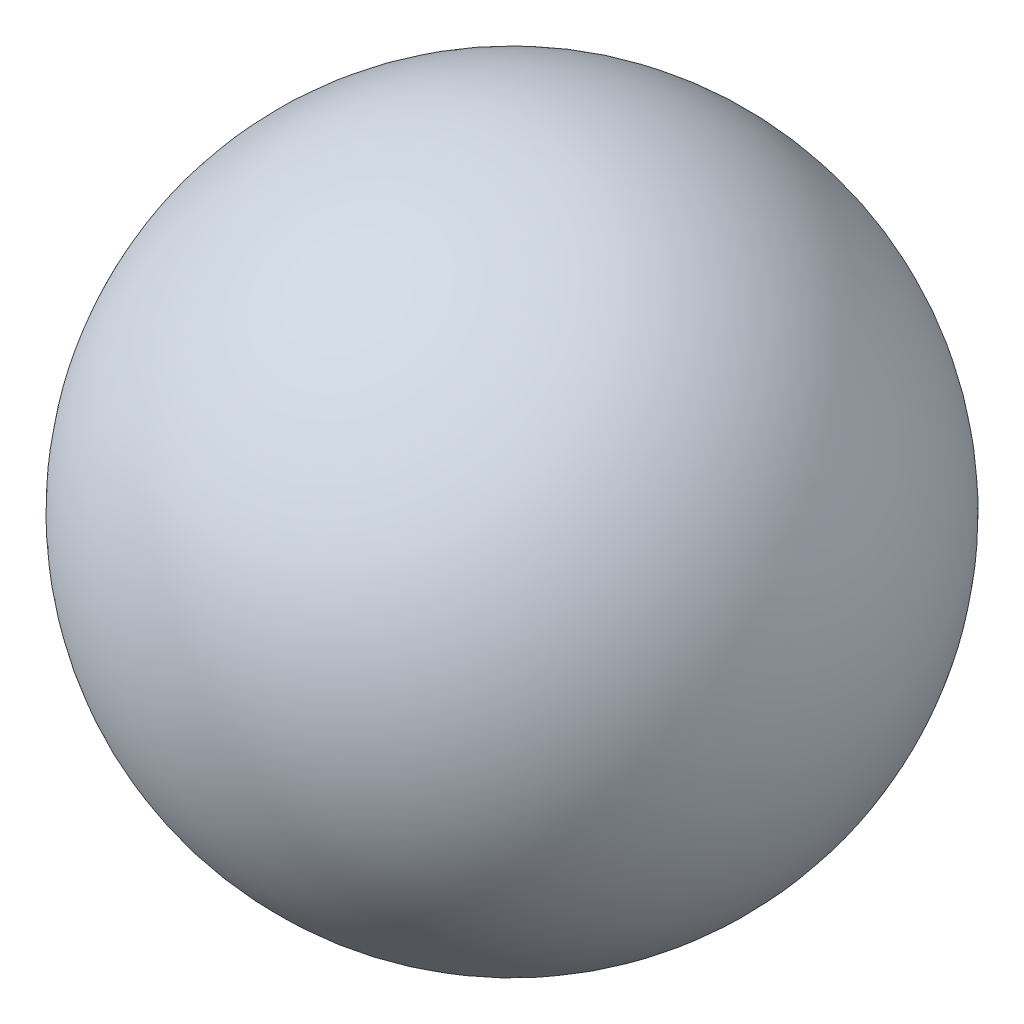
SolidWorks part; units mm, degrees
ref_plane "Front Plane" through (0, 0, 0) normal (0, 0, 1) x (1, 0, 0)
ref_plane "Top Plane" through (0, 0, 0) normal (0, 1, 0) x (1, 0, 0)
ref_plane "Right Plane" through (0, 0, 0) normal (1, 0, 0) x (0, 0, -1)
sketch "Sketch2" plane through (0, 0, 0) normal (0, 1, 0) x (1, 0, 0)
  line L0 (-0.8, 0) -> (0.8, 0) construction
  line L1 (-0.8, 0) -> (0.8, 0)
  arc A0 (0.8, 0) -> (-0.8, 0) centre (0, 0) ccw
  dimension "D1" = 1.6
revolve "Revolve1" add sketch "Sketch2" angle 360 about L0
